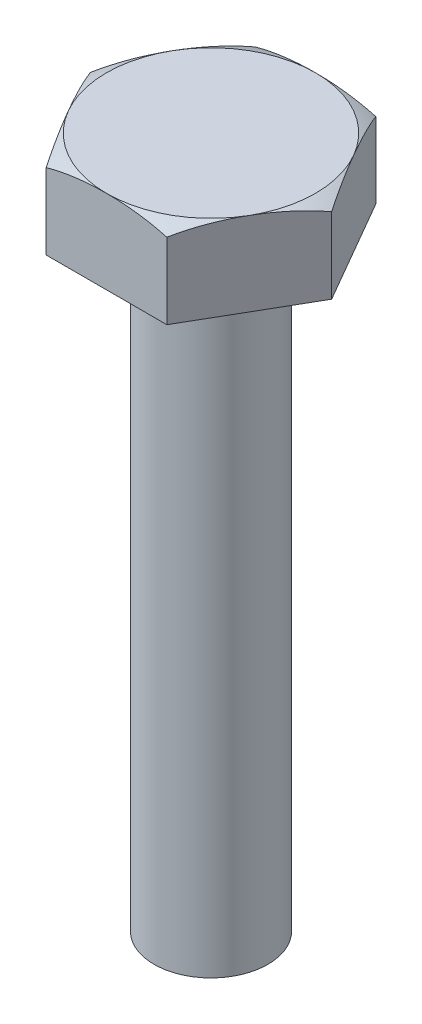
SolidWorks part; units mm, degrees
ref_plane "前视基准面" through (0, 0, 0) normal (0, 0, 1) x (1, 0, 0)
ref_plane "上视基准面" through (0, 0, 0) normal (0, 1, 0) x (1, 0, 0)
ref_plane "右视基准面" through (0, 0, 0) normal (1, 0, 0) x (0, 0, -1)
sketch "草图1" plane through (0, 0, 0) normal (0, 1, 0) x (1, 0, 0)
  line L1 (3.1754, 0) -> (1.5877, 2.75)
  line L2 (1.5877, 2.75) -> (-1.5877, 2.75)
  line L3 (-1.5877, 2.75) -> (-3.1754, 0)
  line L4 (-3.1754, 0) -> (-1.5877, -2.75)
  line L5 (-1.5877, -2.75) -> (1.5877, -2.75)
  line L6 (1.5877, -2.75) -> (3.1754, 0)
  circle A0 centre (0, 0) radius 2.75 construction
  dimension "D1" = 5.5
extrude "凸台-拉伸1" add sketch "草图1" along normal blind 2.2
sketch "草图2" plane through (0, 0, 0) normal (1, 0, 0) x (0, 0, -1)
  line L0 (-2.75, 2.2) -> (-4.95, 2.2)
  line L1 (-4.95, 2.2) -> (-4.95, 0)
  line L2 (0, 0) -> (0, 2.2) construction
  line L3 (-2.75, 2.2) -> (-4.95, 1.2887) construction
  line L4 (-4.95, 2.2) -> (-2.75, 0) construction
  arc A1 (-2.75, 2.2) -> (-4.95, 0) centre (-1.1944, -1.5556) ccw
  dimension "D1" = 22.5
  dimension "D2" = 2.2
  dimension "D3" = 2.2
revolve "切除-旋转1" cut sketch "草图2" angle 360 about L2
sketch "草图3" plane through (0, 0, 0) normal (0, -1, 0) x (1, 0, 0)
  circle A0 centre (0, 0) radius 1.5
extrude "凸台-拉伸2" add sketch "草图3" along normal blind 16
